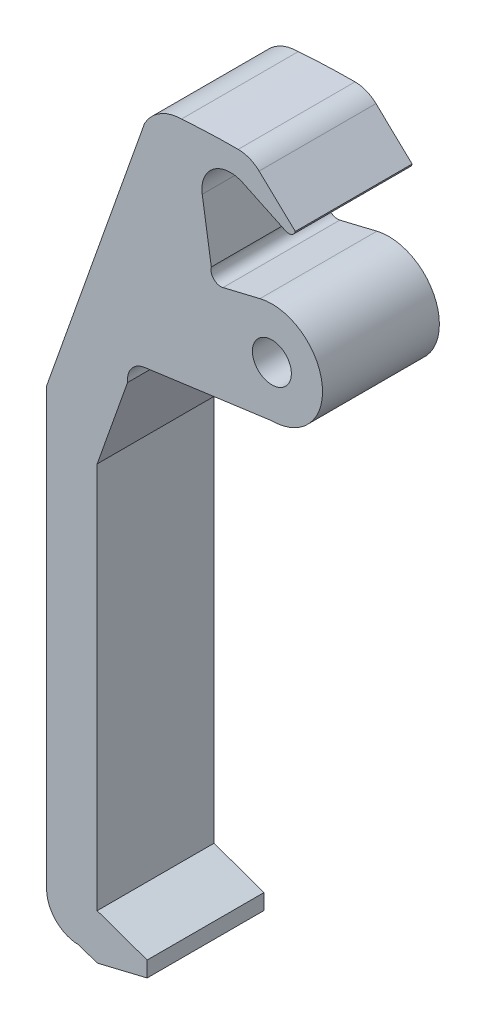
SolidWorks part; units mm, degrees
ref_plane "Plan de face" through (0, 0, 0) normal (0, 0, 1) x (1, 0, 0)
ref_plane "Plan de dessus" through (0, 0, 0) normal (0, 1, 0) x (1, 0, 0)
ref_plane "Plan de droite" through (0, 0, 0) normal (1, 0, 0) x (0, 0, -1)
sketch "Esquisse1" plane through (0, 0, 0) normal (0, 0, 1) x (1, 0, 0)
  line L0 (-4.5157, 5.2242) -> (-4.5157, 8.0474) construction
  line L1 (-5.1256, 7.7529) -> (-7.0256, 7.2946)
  line L2 (-7.6252, 7.9122) -> (-8.0918, 10.9122)
  line L3 (-6.0151, 12.465) -> (-3.7966, 11.4178)
  line L4 (-16.083, -1.6028) -> (-16.083, -23.9882)
  line L6 (-11.0575, 12.571) -> (-16.083, -1.6028)
  line L8 (-11.9273, 0.6219) -> (-13.4868, -3.7764)
  line L9 (-5.1705, 13.4033) -> (-3.314, 11.6469)
  line L11 (-4.5157, 2.6231) -> (-11.0575, 1.7306)
  line L16 (-14.4318, -25.6395) -> (-13.4868, -25.9746)
  line L17 (-13.4868, -25.9746) -> (-10.9207, -25.3556)
  line L18 (-10.9207, -25.3556) -> (-10.9207, -24.5562)
  line L19 (-10.9207, -24.5562) -> (-13.4868, -23.6463)
  line L20 (-13.4868, -3.7764) -> (-13.4868, -23.6463)
  circle A0 centre (-4.5157, 5.2242) radius 1
  arc A1 (-5.1256, 7.7529) -> (-4.5157, 2.6231) centre (-4.5157, 5.2242) cw
  arc A3 (-7.0256, 7.2946) -> (-7.6252, 7.9122) centre (-7.1428, 7.7806) cw
  arc A4 (-8.0918, 10.9122) -> (-6.0151, 12.465) centre (-6.6416, 11.1378) cw
  arc A5 (-3.7966, 11.4178) -> (-3.314, 11.6469) centre (-3.6492, 11.7301) ccw
  arc A6 (-5.1705, 13.4033) -> (-6.2461, 13.8315) centre (-6.2461, 12.2664) ccw
  arc A7 (-9.1576, 13.724) -> (-11.0575, 12.571) centre (-9.1412, 11.5552) ccw
  arc A8 (-6.2461, 13.8315) -> (-9.1576, 13.724) centre (-6.2461, -25.6395) ccw
  arc A9 (-11.0575, 1.7306) -> (-11.9273, 0.6219) centre (-10.9207, 0.7277) ccw
  arc A11 (-16.083, -23.9882) -> (-14.4318, -25.6395) centre (-14.4318, -23.9882) ccw
  dimension "D1" = 1.9
  dimension "D2" = 0.5
  dimension "D3" = 2
  dimension "D4" = 3
extrude "Boss.-Extru.1" add sketch "Esquisse1" along normal blind 6
